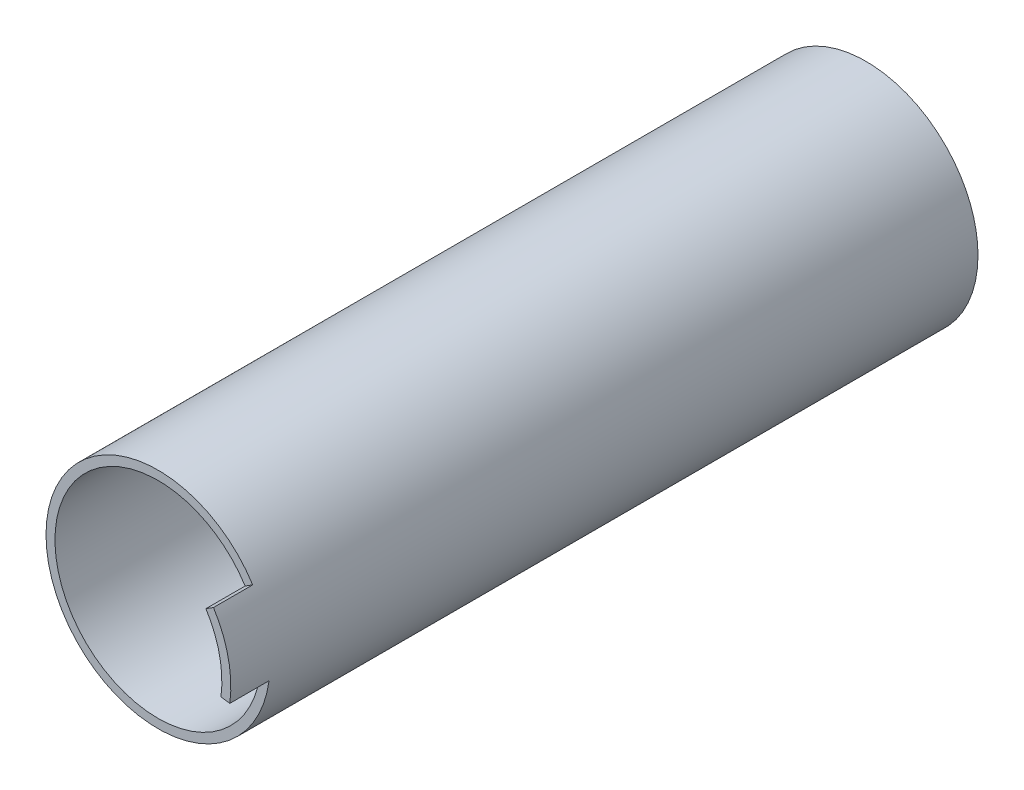
SolidWorks part; units mm, degrees
ref_plane "Спереди" through (0, 0, 0) normal (0, 0, 1) x (1, 0, 0)
ref_plane "Сверху" through (0, 0, 0) normal (0, 1, 0) x (1, 0, 0)
ref_plane "Справа" through (0, 0, 0) normal (1, 0, 0) x (0, 0, -1)
sketch "Эскиз2" plane through (0, 0, 0) normal (0, 0, 1) x (1, 0, 0)
  circle A0 centre (0, 0) radius 20
  circle A1 centre (0, 0) radius 18.4
  dimension "D1" = 40
  dimension "D2" = 36.8
extrude "Бобышка-Вытянуть1" add sketch "Эскиз2" along normal blind 126.4
sketch "Эскиз5" plane through (0, 0, 0) normal (0, 0, -1) x (-1, 0, 0)
  line L0 (0, 0) -> (0, 18.4) construction
  line L1 (0, 0) -> (2.99, 18.1554) construction
  line L2 (0, 18.4) -> (0, 9.2195)
  line L3 (2.99, 18.1554) -> (1.4982, 9.097)
  circle A0 centre (0, 0) radius 18.4 construction
  arc A1 (0, 18.4) -> (2.99, 18.1554) centre (0, 0) cw
  arc A2 (1.4982, 9.097) -> (3.372, 3.6918) centre (7.4184, 8.122) ccw
  circle A3 centre (0, 0) radius 3
  arc A4 (-2.7273, 4.1907) -> (3.372, 3.6918) centre (0, 0) ccw
  arc A5 (0, 9.2195) -> (-2.7273, 4.1907) centre (-6, 9.2195) cw
  point P16 (0, 5)
  dimension "D2" = 5
  dimension "D3" = 6
  dimension "D4" = 6
  dimension "D1" = 3
extrude "Бобышка-Вытянуть3" add sketch "Эскиз5" against normal through all
sketch "Sketch1" plane through (0, 0, 0) normal (0, 0, -1) x (-1, 0, 0)
  line L0 (0.6125, 18.3898) -> (2.99, 18.1554)
  arc A2 (0.6125, 18.3898) -> (2.99, 18.1554) centre (0, 0) ccw
  point P0 (0, 0)
extrude "Cut-Extrude1" cut sketch "Sketch1" against normal blind 59
sketch "Sketch2" plane through (0, 0, 126.4) normal (0, 0, 1) x (1, 0, 0)
  line L0 (-0.6125, 18.3898) -> (-2.99, 18.1554)
  arc A2 (-0.6125, 18.3898) -> (-2.99, 18.1554) centre (0, 0) cw
  point P0 (0, 0)
extrude "Cut-Extrude2" cut sketch "Sketch2" against normal blind 59
sketch "Sketch3" plane through (0, 0, 0) normal (0, 0, 1) x (1, 0, 0)
  line L0 (5, 0) -> (5, 16.6661)
  line L1 (-5, 0) -> (-5, 16.6661)
  circle A0 centre (0, 0) radius 5 construction
  circle A1 centre (0, 0) radius 3
  arc A2 (5, 0) -> (-5, 0) centre (0, 0) cw
  arc A3 (5, 16.6661) -> (-5, 16.6661) centre (0, 0) ccw
  arc A4 (-2.99, 18.1554) -> (-0.6125, 18.3898) centre (0, 0) ccw construction
  dimension "D1" = 10
  dimension "D2" = 6
  dimension "D3" = 1
sketch "Sketch6" plane through (0, 0, 126.4) normal (0, 0, 1) x (1, 0, 0)
  line L0 (20, 0) -> (0, 0) construction
  line L2 (0, 0) -> (19.8206, -2.6728) construction
  line L3 (0, 0) -> (16.9015, 10.6929) construction
  line L4 (16.9015, 10.6929) -> (15.5494, 9.8375)
  line L5 (19.8206, -2.6728) -> (18.235, -2.459)
  circle A1 centre (0, 0) radius 20 construction
  arc A3 (16.9015, 10.6929) -> (19.8206, -2.6728) centre (0, 0) cw
  arc A5 (15.5494, 9.8375) -> (18.235, -2.459) centre (0, 0) cw
  arc A6 (-2.99, 18.1554) -> (-0.6125, 18.3898) centre (0, 0) ccw construction
  dimension "D1" = 40
  dimension "D2" = 7.68
extrude "Boss-Extrude4" add sketch "Sketch6" along normal blind 7
extrude "Boss-Extrude6" add sketch "Sketch3" along normal offset from surface (58.6 mm away) 0.4 separate body up to face at (-0.7097, 10.2341, 59)
